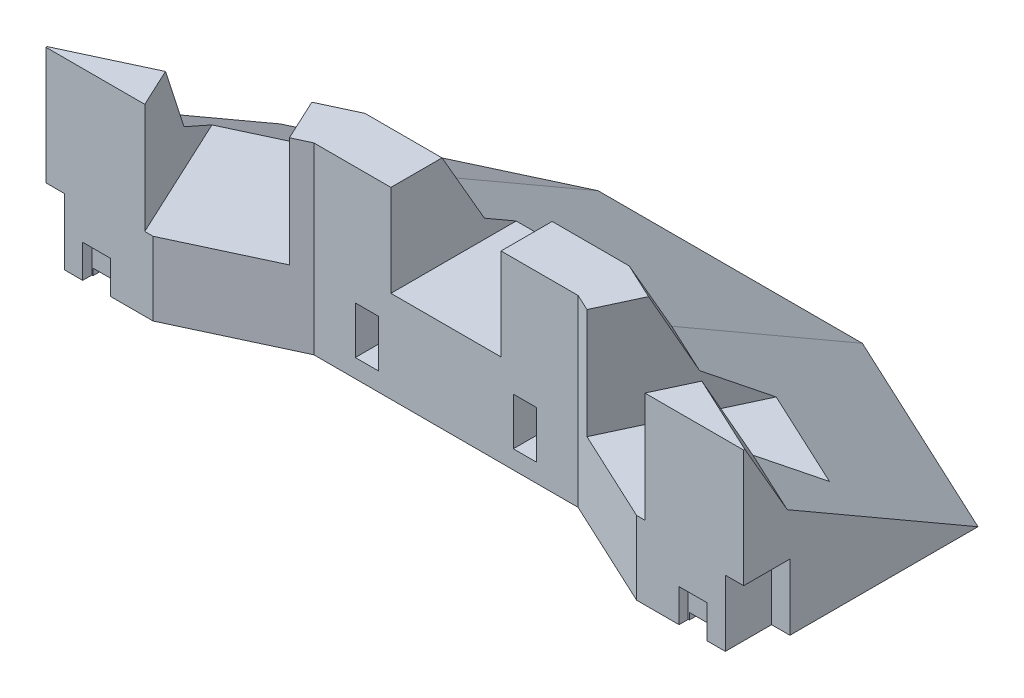
SolidWorks part; units mm, degrees
material "Nailon 101"
ref_plane "Alzado" through (0, 0, 0) normal (0, 0, 1) x (1, 0, 0)
ref_plane "Planta" through (0, 0, 0) normal (0, 1, 0) x (1, 0, 0)
ref_plane "Vista lateral" through (0, 0, 0) normal (1, 0, 0) x (0, 0, -1)
sketch "Croquis1" plane through (0, 0, 0) normal (0, 1, 0) x (1, 0, 0)
  line L0 (-96.8307, 0) -> (96.8307, 0)
  line L1 (0, 0) -> (0, 91.3658) construction
  line L2 (-36, 91.3658) -> (36, 91.3658)
  line L3 (96.8307, 0) -> (96.8307, 63)
  line L4 (-96.8307, 0) -> (-96.8307, 63)
  line L5 (-96.8307, 63) -> (-36, 91.3658)
  line L6 (36, 91.3658) -> (96.8307, 63)
  point P4 (0, 0)
  point P10 (0, 91.3658)
  dimension "D1" = 155
  dimension "D2" = 155
  dimension "D3" = 67.1193
  dimension "D4" = 193.6615
  dimension "D5" = 63
extrude "Saliente-Extruir1" add sketch "Croquis1" along normal blind 50
sketch3d "Croquis3D2"
  line L0 (-36, 0, -91.3658) -> (-36, 30, -39.4043)
  line L4 (-36, 61.7827, -21.0546) -> (-36, 61.7827, -91.3658)
  line L5 (-36, 30, -39.4043) -> (-36, 61.7827, -21.0546)
  line L6 (-36, 61.7827, -91.3658) -> (-36, 0, -91.3658)
  line L7 (-36, 0, -91.3658) -> (-36, 0, -41.93) construction
  point P6 (-36, 50, 0)
  dimension "D1" = 30
  dimension "D2" = 60
  dimension "D3" = 150
extrude "Cortar-Extruir1" cut sketch "Croquis3D2" along direction (-1, 0, 0) on the side against the normal blind 72
sketch "Croquis2" plane through (36, 0, 0) normal (-1, 0, 0) x (0, 0, 1)
  line L0 (-91.3658, 50) -> (-27.8573, 50)
  line L1 (-27.8573, 50) -> (-39.4043, 30)
  line L2 (-39.4043, 30) -> (-91.3658, 0)
  line L3 (-91.3658, 0) -> (-91.3658, 50)
sweep "Cortar-Barrer1" cut profiles "Croquis2" path edge at (66.4154, 50, -77.1829)
sketch "Croquis3" plane through (-36, 0, 0) normal (1, 0, 0) x (0, 0, -1)
  line L0 (27.8573, 50) -> (91.3658, 50)
  line L1 (91.3658, 50) -> (91.3658, 0)
  line L2 (91.3658, 0) -> (39.4043, 30)
  line L3 (39.4043, 30) -> (27.8573, 50)
sweep "Cortar-Barrer2" cut profiles "Croquis3" path edge at (-66.4154, 50, -77.1829)
sketch "Croquis6" plane through (0, 0, 0) normal (0, 0, 1) x (1, 0, 0)
  line L0 (-96.8307, 49.1192) -> (-36, 49.1192) construction
  line L1 (-36, 49.1192) -> (36, 49.1192) construction
  line L2 (36, 49.1192) -> (96.8307, 49.1192) construction
  line L3 (-36, 50) -> (-36, 0) construction
  line L4 (-96.8307, 0) -> (96.8307, 0) construction
  line L5 (36, 50) -> (36, 0) construction
  line L6 (-95.7402, 50) -> (95.7402, 50) construction
  line L7 (-15, 50) -> (15, 50)
  line L8 (-15, 50) -> (-15, 25)
  line L9 (-15, 25) -> (15, 25)
  line L10 (15, 50) -> (15, 25)
  dimension "D1" = 21
  dimension "D2" = 21
  dimension "D3" = 25
extrude "Cortar-Extruir4" cut sketch "Croquis6" against normal up to next
sketch "Croquis7" plane through (0, 50, 0) normal (0, 1, 0) x (1, 0, 0)
  line L0 (-15, 0) -> (-15, 13.9287) construction
  line L1 (-15, 27.8573) -> (-15, 0) construction
  line L2 (15, 0) -> (15, 13.9287) construction
  line L3 (15, 27.8573) -> (15, 0) construction
  line L4 (-15, 13.9287) -> (15, 13.9287) construction
  line L5 (36, 27.8573) -> (36, 18.3573) construction
  line L6 (-36, 27.8573) -> (-36, 18.3573) construction
  line L7 (-36, 13.9287) -> (36, 13.9287)
  line L8 (-36, 13.9287) -> (-81.028, -7.0682) construction
  line L10 (36, 13.9287) -> (94.1708, -13.1968) construction
  line L11 (36, 13.9287) -> (65.8701, 0)
  line L12 (15, 0) -> (95.7402, 0) construction
  line L13 (-36, 13.9287) -> (-65.8701, 0)
  line L14 (-95.7402, 0) -> (-15, 0) construction
  line L15 (-65.8701, 0) -> (65.8701, 0)
  point P13 (0, 13.9287)
  dimension "D1" = 155
  dimension "D2" = 155
extrude "Cortar-Extruir5" cut sketch "Croquis7" against normal up to next
sketch "Croquis8" plane through (-11.7648, 0, -25.2297) normal (0.4226, 0, 0.9063) x (0.9063, 0, -0.4226)
  line L0 (-26.7406, 50) -> (-31.7406, 50) construction
  line L1 (-26.7406, 50) -> (-59.6986, 50) construction
  line L3 (-31.7406, 50) -> (-61.7406, 50)
  line L4 (-31.7406, 50) -> (-31.7406, 20)
  line L5 (-31.7406, 20) -> (-61.7406, 20)
  line L6 (-61.7406, 50) -> (-61.7406, 20)
  dimension "D1" = 30
  dimension "D2" = 5
  dimension "D3" = 30
extrude "Cortar-Extruir6" cut sketch "Croquis8" against normal blind 40 contours L4 L5 L6 L3
sketch "Croquis9" plane through (11.7648, 0, -25.2297) normal (-0.4226, 0, 0.9063) x (0.9063, 0, 0.4226)
  line L0 (26.7406, 50) -> (31.7406, 50) construction
  line L1 (59.6986, 50) -> (26.7406, 50) construction
  line L3 (31.7406, 50) -> (61.7406, 50)
  line L4 (31.7406, 50) -> (31.7406, 20)
  line L5 (31.7406, 20) -> (61.7406, 20)
  line L6 (61.7406, 50) -> (61.7406, 20)
  dimension "D1" = 5
  dimension "D2" = 30
  dimension "D3" = 30
extrude "Cortar-Extruir7" cut sketch "Croquis9" against normal blind 40
sketch "Croquis10" plane through (0, 0, -13.9287) normal (0, 0, 1) x (1, 0, 0)
  line L0 (15, 25) -> (18.35, 25) construction
  line L1 (-15, 25) -> (-18.35, 25) construction
  line L11 (-18.35, 0) -> (-24.7, 0) construction
  line L12 (36, 0) -> (-36, 0) construction
  line L13 (-24.7, 0) -> (-24.7, 5.0014) construction
  line L14 (-24.7, 5.0014) -> (-18.35, 5.0014) construction
  line L15 (-18.35, 5.0014) -> (-18.35, 0) construction
  line L16 (18.35, 0) -> (18.35, 5.0014) construction
  line L17 (-18.35, 5.0014) -> (-24.7, 5.0014)
  line L18 (-18.35, 5.0014) -> (-18.35, 17.9014)
  line L19 (-18.35, 17.9014) -> (-24.7, 17.9014)
  line L20 (-24.7, 5.0014) -> (-24.7, 17.9014)
  line L21 (18.35, 5.0014) -> (24.7, 5.0014) construction
  line L22 (24.7, 5.0014) -> (24.7, 0) construction
  line L23 (24.7, 0) -> (18.35, 0) construction
  line L25 (24.7, 5.0014) -> (18.35, 5.0014)
  line L26 (24.7, 5.0014) -> (24.7, 17.9014)
  line L27 (24.7, 17.9014) -> (18.35, 17.9014)
  line L28 (18.35, 5.0014) -> (18.35, 17.9014)
  dimension "D1" = 3.35
  dimension "D3" = 6.35
  dimension "D4" = 12.9
  dimension "D6" = 6.35
  dimension "D7" = 12.9
extrude "Cortar-Extruir8" cut sketch "Croquis10" against normal blind 33
sketch "Croquis12" plane through (0, 50, 0) normal (0, 1, 0) x (1, 0, 0)
  line L0 (-96.8307, 0) -> (-95.0307, 0)
  line L1 (-95.7402, 0) -> (-68.1232, 0) construction
  line L2 (-95.0307, 0) -> (-95.0307, 63.8394)
  line L3 (-36, 91.3658) -> (-96.8307, 63) construction
  line L4 (-95.0307, 63.8394) -> (-96.8307, 63)
  line L5 (-96.8307, 63) -> (-96.8307, 0)
  dimension "D1" = 1.8
extrude "Cortar-Extruir9" cut sketch "Croquis12" against normal up to next
sketch "Croquis13" plane through (0, 50, 0) normal (0, 1, 0) x (1, 0, 0)
  line L0 (96.8307, 0) -> (95.0321, 0)
  line L1 (68.1232, 0) -> (95.7402, 0) construction
  line L2 (95.0321, 0) -> (95.0321, 63.8387)
  line L3 (96.8307, 63) -> (36, 91.3658) construction
  line L4 (95.0321, 63.8387) -> (96.8307, 63)
  line L5 (96.8307, 63) -> (96.8307, 0)
extrude "Cortar-Extruir10" cut sketch "Croquis13" against normal up to next and the other way through all
sketch "Croquis14" plane through (95.0321, 0, 0) normal (1, 0, 0) x (0, 0, -1)
  line L1 (0, 0) -> (12.6, 0)
  line L2 (0, 0) -> (0, 18)
  line L3 (0, 18) -> (12.6, 18)
  line L4 (12.6, 0) -> (12.6, 18)
  dimension "D1" = 18
  dimension "D2" = 12.6
extrude "Cortar-Extruir11" cut sketch "Croquis14" against normal blind 5 contours L3 L4 L1 L2
sketch "Croquis15" plane through (-95.0307, 0, 0) normal (-1, 0, 0) x (0, 0, 1)
  line L1 (0, 0) -> (-12.5178, 0)
  line L2 (0, 0) -> (0, 18.0014)
  line L3 (0, 18.0014) -> (-12.5178, 18.0014)
  line L4 (-12.5178, 0) -> (-12.5178, 18.0014)
  dimension "D1" = 12.5178
extrude "Cortar-Extruir12" cut sketch "Croquis15" against normal blind 5
sketch "Croquis16" plane through (0, 0, 0) normal (0, -1, 0) x (1, 0, 0)
  line L0 (-90.0307, 0) -> (-85.0307, 0) construction
  line L1 (-90.0307, 0) -> (-65.8701, 0) construction
  line L2 (90.0321, 0) -> (85.0321, 0) construction
  line L4 (65.8701, 0) -> (90.0321, 0) construction
  line L10 (-85.0307, 0) -> (-77.4307, 0)
  line L11 (-85.0307, 0) -> (-85.0307, -2.5)
  line L12 (-85.0307, -2.5) -> (-77.4307, -2.5)
  line L13 (-77.4307, 0) -> (-77.4307, -2.5)
  line L14 (85.0321, 0) -> (77.4321, 0)
  line L15 (85.0321, 0) -> (85.0321, -2.5)
  line L16 (85.0321, -2.5) -> (77.4321, -2.5)
  line L17 (77.4321, 0) -> (77.4321, -2.5)
  dimension "D1" = 5
  dimension "D2" = 5
  dimension "D3" = 7.6
  dimension "D4" = 2.5
  dimension "D5" = 2.5
  dimension "D6" = 7.6
extrude "Cortar-Extruir13" cut sketch "Croquis16" against normal blind 9
sketch "Croquis17" plane through (0, 0, 0) normal (0, -1, 0) x (1, 0, 0)
  line L0 (-81.2307, 0) -> (-81.2307, -18.618) construction
  line L1 (-77.4307, 0) -> (-85.0307, 0) construction
  line L2 (-81.2307, -2.5) -> (-84.7307, -2.5)
  line L3 (-85.0307, -2.5) -> (-77.4307, -2.5) construction
  line L4 (-81.2307, -2.5) -> (-77.7307, -2.5)
  line L5 (-84.7307, -2.5) -> (-84.7307, -13.5)
  line L6 (-84.7307, -13.5) -> (-77.7307, -13.5)
  line L7 (-77.7307, -13.5) -> (-77.7307, -2.5)
  line L8 (0, -13.9287) -> (0, -54.2238) construction
  line L9 (36, -13.9287) -> (-36, -13.9287) construction
  line L10 (81.2307, 0) -> (81.2307, -18.618) construction
  line L11 (77.7307, -13.5) -> (77.7307, -2.5)
  line L12 (84.7307, -13.5) -> (77.7307, -13.5)
  line L13 (84.7307, -2.5) -> (84.7307, -13.5)
  line L14 (81.2307, -2.5) -> (77.7307, -2.5)
  line L15 (81.2307, -2.5) -> (84.7307, -2.5)
  dimension "D1" = 3.5
  dimension "D2" = 3.5
  dimension "D3" = 11
extrude "Cortar-Extruir14" cut sketch "Croquis17" against normal blind 1.8
